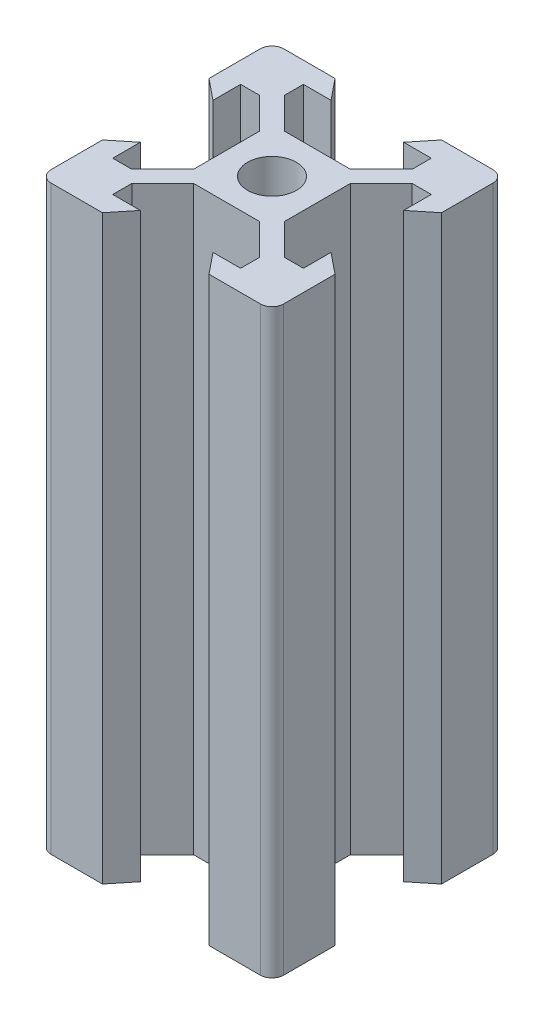
SolidWorks part; units mm, degrees
ref_plane "Front Plane" through (0, 0, 0) normal (0, 0, 1) x (1, 0, 0)
ref_plane "Top Plane" through (0, 0, 0) normal (0, 1, 0) x (1, 0, 0)
ref_plane "Right Plane" through (0, 0, 0) normal (1, 0, 0) x (0, 0, -1)
sketch "Sketch1" plane through (0, 0, 0) normal (0, 1, 0) x (1, 0, 0)
  line L0 (-3.125, 8.2) -> (-4.58, 10)
  line L1 (-9, 10) -> (9, 10)
  line L2 (-10, 9) -> (-10, -9)
  line L3 (-9, -10) -> (9, -10)
  line L4 (10, 9) -> (10, -9)
  line L5 (-10, 10) -> (10, -10) construction
  line L6 (-10, -10) -> (10, 10) construction
  line L7 (-10, 0) -> (0, 0) construction
  line L8 (0, 10) -> (0, 0) construction
  line L9 (-8.2, 3.125) -> (-10, 4.58)
  line L10 (-8.2, 3.125) -> (-8.2, 5.5)
  line L11 (-3.125, 8.2) -> (-5.5, 8.2)
  line L12 (-5.5, 8.2) -> (-5.5, 6.56)
  line L13 (-2.84, 3.9) -> (2.84, 3.9)
  line L14 (-5.5, 6.56) -> (-2.84, 3.9)
  line L15 (-8.2, 5.5) -> (-6.56, 5.5)
  line L16 (-6.56, 5.5) -> (-3.9, 2.84)
  line L17 (-3.9, 2.84) -> (-3.9, -2.84)
  line L18 (3.9, 2.84) -> (3.9, -2.84)
  line L19 (6.56, 5.5) -> (3.9, 2.84)
  line L20 (8.2, 5.5) -> (6.56, 5.5)
  line L21 (8.2, 3.125) -> (8.2, 5.5)
  line L22 (8.2, 3.125) -> (10, 4.58)
  line L23 (3.125, 8.2) -> (4.58, 10)
  line L24 (3.125, 8.2) -> (5.5, 8.2)
  line L25 (5.5, 8.2) -> (5.5, 6.56)
  line L26 (5.5, 6.56) -> (2.84, 3.9)
  line L27 (-8.2, -3.125) -> (-10, -4.58)
  line L28 (-8.2, -3.125) -> (-8.2, -5.5)
  line L29 (-8.2, -5.5) -> (-6.56, -5.5)
  line L30 (-6.56, -5.5) -> (-3.9, -2.84)
  line L31 (8.2, -3.125) -> (10, -4.58)
  line L32 (8.2, -3.125) -> (8.2, -5.5)
  line L33 (8.2, -5.5) -> (6.56, -5.5)
  line L34 (6.56, -5.5) -> (3.9, -2.84)
  line L35 (5.5, -6.56) -> (2.84, -3.9)
  line L36 (5.5, -8.2) -> (5.5, -6.56)
  line L37 (3.125, -8.2) -> (5.5, -8.2)
  line L38 (3.125, -8.2) -> (4.58, -10)
  line L39 (-5.5, -6.56) -> (-2.84, -3.9)
  line L40 (-2.84, -3.9) -> (2.84, -3.9)
  line L41 (-5.5, -8.2) -> (-5.5, -6.56)
  line L42 (-3.125, -8.2) -> (-5.5, -8.2)
  line L43 (-3.125, -8.2) -> (-4.58, -10)
  circle A0 centre (0, 0) radius 2.1
  arc A1 (-10, -9) -> (-9, -10) centre (-9, -9) ccw
  arc A2 (9, -10) -> (10, -9) centre (9, -9) ccw
  arc A3 (9, 10) -> (10, 9) centre (9, 9) cw
  arc A4 (-9, 10) -> (-10, 9) centre (-9, 9) ccw
  point P0 (0, 0)
  point P35 (0, 3.9)
  point P40 (-3.9, 0)
  point P41 (3.9, 0)
  dimension "D3" = 4.2
  dimension "D2" = 1
  dimension "D1" = 20
  dimension "D4" = 6.1
  dimension "D5" = 6.25
  dimension "D6" = 11
  dimension "D7" = 5.68
  dimension "D8" = 9.16
  dimension "D9" = 1.8
extrude "Boss-Extrude1" add sketch "Sketch1" along normal blind 50 contours L43 L42 L41 L39 L40 L35 L36 L37 L38 L3 L4 L31 L32 L33 L34 L18 L19 L20 L21 L22 L1 L23 L24 L25 L26 L13 L14 L12 L11 L0 L2 L9 L10 L15 L16 L17 L30 L29 L28 L27 A0
